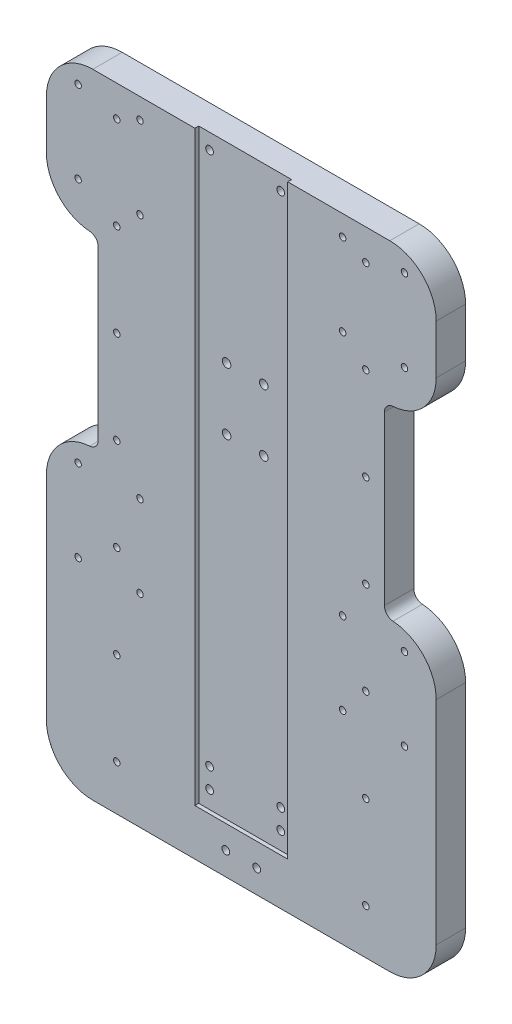
SolidWorks part; units mm, degrees
ref_plane "Piano frontale" through (0, 0, 0) normal (0, 0, 1) x (1, 0, 0)
ref_plane "Piano superiore" through (0, 0, 0) normal (0, 1, 0) x (1, 0, 0)
ref_plane "Piano destro" through (0, 0, 0) normal (1, 0, 0) x (0, 0, -1)
sketch "Schizzo1" plane through (0, 0, 0) normal (0, 0, 1) x (1, 0, 0)
  line L1 (126, -250) -> (-126, -250)
  line L2 (126, -250) -> (126, 250)
  line L3 (126, 250) -> (-126, 250)
  line L4 (-126, -250) -> (-126, 250)
  line L5 (126, -250) -> (-126, 250) construction
  line L6 (126, 250) -> (-126, -250) construction
  point P0 (0, 0)
  dimension "D1" = 252
  dimension "D2" = 500
extrude "Estrusione-Estrusione1" add sketch "Schizzo1" along normal blind 19
sketch "Schizzo2" plane through (0, 0, 19) normal (0, 0, 1) x (1, 0, 0)
  line L0 (1265.2426, 21.4119) -> (-695.7574, 21.4119) construction
  line L1 (1265.2426, 13.5541) -> (-695.7574, 13.5541) construction
  line L2 (1265.2426, 53.5541) -> (-695.7574, 53.5541) construction
  line L3 (1265.2426, 61.4119) -> (-695.7574, 61.4119) construction
  line L4 (-126, 250) -> (-126, -250)
  line L5 (-126, -250) -> (126, -250)
  line L6 (126, -250) -> (126, 250)
  line L7 (126, 250) -> (-126, 250)
  line L8 (-126, 250) -> (-126, -250) construction
  line L9 (-126, -250) -> (126, -250) construction
  line L10 (126, -250) -> (126, 250) construction
  line L11 (126, 250) -> (-126, 250) construction
  line L12 (1265.2426, 21.4119) -> (-695.7574, 21.4119) construction
  line L13 (1265.2426, 13.5541) -> (-695.7574, 13.5541) construction
  line L14 (1265.2426, 53.5541) -> (-695.7574, 53.5541) construction
  line L15 (1265.2426, 61.4119) -> (-695.7574, 61.4119) construction
  line L16 (126, -45.017) -> (-126, -45.017) construction
  line L17 (126, -25.017) -> (-126, -25.017) construction
  line L18 (126, -45.017) -> (-126, -45.017) construction
  line L19 (126, -25.017) -> (-126, -25.017) construction
  line L20 (-126, -45.017) -> (-126, -25.017) construction
  line L21 (126, -35.017) -> (-126, -35.017) construction
  line L22 (-126, -45.017) -> (126, -45.017) construction
  line L23 (-126, -45.017) -> (-126, -25.017) construction
  line L24 (-126, -25.017) -> (126, -25.017) construction
  line L25 (126, -45.017) -> (126, -25.017) construction
  circle A0 centre (110, 17.483) radius 3.9289
  circle A1 centre (110, 57.483) radius 3.9289
  circle A2 centre (-110, 17.483) radius 3.9289
  circle A3 centre (-110, 57.483) radius 3.9289
  circle A4 centre (110, -35.017) radius 3.5
  circle A5 centre (-110, -35.017) radius 3.5
  circle A6 centre (55, -35.017) radius 3.5
  circle A8 centre (-55, -35.017) radius 3.5
  circle A9 centre (20, -35.017) radius 3.5
  circle A10 centre (-20, -35.017) radius 3.5
  circle A11 centre (165, -35.017) radius 3.5 [skipped]
  dimension "D2" = 16
  dimension "D3" = 7.8579
  dimension "D4" = 16
  dimension "D5" = 7.8579
  dimension "D6" = 7
  dimension "D7" = 7
  dimension "D8" = 2
  dimension "D1" = 0
  dimension "D9" = 2
  dimension "D10" = 2
  dimension "D11" = 2
sketch "Schizzo3" plane through (0, 250, 0) normal (0, 1, 0) x (1, 0, 0)
  line L0 (126, -19) -> (-126, -19) construction
  line L1 (30, -16.5) -> (-30, -16.5)
  line L2 (30, -16.5) -> (30, -19)
  line L3 (30, -19) -> (-30, -19)
  line L4 (-30, -16.5) -> (-30, -19)
  line L5 (126, -19) -> (126, 0) construction
  line L6 (-126, -19) -> (-126, 0) construction
  line L7 (126, -19) -> (-126, -19) construction
  dimension "D1" = 2.5
  dimension "D2" = 96
  dimension "D3" = 96
extrude "Taglio-Estrusione1" cut sketch "Schizzo3" against normal through all
sketch "Schizzo4" plane through (0, 0, 16.5) normal (0, 0, 1) x (1, 0, 0)
  line L0 (30, -250) -> (30, 250) construction
  line L2 (30, 250) -> (-30, 250) construction
  line L3 (30, -250) -> (30, 250) construction
  line L6 (-30, 250) -> (-126, 250) construction
  line L7 (-30, -250) -> (-30, 250) construction
  point P11 (23, -118)
  point P14 (-23, -118)
  point P15 (-23, -105)
  point P16 (23, -105)
  point P17 (23, 240)
  point P18 (-23, 240)
  dimension "D1" = 46
  dimension "D2" = 13
  dimension "D3" = 13
  dimension "D4" = 46
  dimension "D5" = 7
  dimension "D6" = 345
  dimension "D7" = 10
  dimension "D8" = 46
  dimension "D9" = 7
  dimension "D10" = 10
  dimension "D11" = 7
  dimension "D12" = 7
sketch "Schizzo5" plane through (0, 0, 19) normal (0, 0, 1) x (1, 0, 0)
  point P4 (80.5006, 170)
  point P7 (80.5006, 110)
  point P16 (80.5006, 50)
  point P17 (80.5006, -10)
  point P18 (80.5006, -70)
  point P19 (80.5006, -130)
  point P20 (80.5006, 230)
hole_wizard "Tap Drill for M5 Tap2" positions "Sketch7" profile "Sketch8" hole size "M5" standard "ISO"
sketch "Sketch7" plane through (0, 0, 19) normal (0, 0, 1) x (1, 0, 0)
  point P0 (80.5006, -130)
  point P3 (80.5006, -70)
  point P7 (80.5006, -10)
  point P10 (80.5006, 50)
  point P13 (80.5006, 110)
  point P16 (80.5006, 170)
  point P19 (80.5006, 230)
sketch "Sketch8" plane through (80.5006, -130, 19) normal (1, 0, 0) x (0, -1, 0)
  line L0 (0, 0) -> (0, 37.8618)
  line L1 (0, 37.8618) -> (2.1, 36.6)
  line L2 (2.1, 36.6) -> (2.1, 0)
  line L5 (2.1, 0) -> (0, 0)
  line L10 (0, 37.8618) -> (-2.1, 36.6) construction
  line L11 (0, -6.35) -> (0, 107.95) construction
  dimension "Hole Dia." = 4.2
  dimension "Hole Depth" = 36.6
  dimension "Drill Angle" = 118
sketch "Schizzo6" plane through (0, 0, 19) normal (0, 0, 1) x (1, 0, 0)
  line L0 (126, -250) -> (126, 250) construction
  line L2 (126, 250) -> (30, 250) construction
  point P23 (108, 172.8083)
  point P26 (63, 172.8083)
  point P27 (63, 229.8083)
  point P28 (108, 229.8083)
  dimension "D1" = 45
  dimension "D2" = 45
  dimension "D3" = 57
  dimension "D4" = 57
  dimension "D5" = 18
  dimension "D6" = 20.1917
  dimension "D7" = 20.1917
  dimension "D8" = 18
hole_wizard "Tap Drill for M5 Tap1" positions "Sketch14" profile "Sketch15" hole size "M5" standard "ISO"
sketch "Sketch14" plane through (0, 0, 19) normal (0, 0, 1) x (1, 0, 0)
  line L1 (105.5, 183.8083) -> (65.5, 183.8083)
  line L2 (105.5, 183.8083) -> (105.5, 236.8083)
  line L3 (105.5, 236.8083) -> (65.5, 236.8083)
  line L4 (65.5, 183.8083) -> (65.5, 236.8083)
  line L6 (105.5, -28.1917) -> (65.5, -28.1917)
  line L7 (105.5, -28.1917) -> (105.5, 24.8083)
  line L8 (105.5, 24.8083) -> (65.5, 24.8083)
  line L9 (65.5, -28.1917) -> (65.5, 24.8083)
  line L10 (85.5, -28.1917) -> (85.5, 236.8083) construction
  line L12 (105.5, 210.3083) -> (65.5, 210.3083) construction
  line L14 (105.5, -1.6917) -> (65.5, -1.6917) construction
  line L16 (108, 172.8083) -> (63, 172.8083) construction
  line L18 (85.5, 256.2745) -> (85.5, -301.4126) construction
  point P19 (105.5, 236.8083)
  point P21 (65.5, 236.8083)
  point P23 (105.5, 183.8083)
  point P25 (65.5, 183.8083)
  point P99 (105.5, -28.1917)
  point P102 (65.5, -28.1917)
  point P105 (65.5, 24.8083)
  point P108 (105.5, 24.8083)
  dimension "D1" = 40
  dimension "D2" = 53
  dimension "D3" = 40
  dimension "D4" = 53
sketch "Sketch15" plane through (105.5, 236.8083, 19) normal (1, 0, 0) x (0, -1, 0)
  line L0 (0, 0) -> (0, 37.8618)
  line L1 (0, 37.8618) -> (2.1, 36.6)
  line L2 (2.1, 36.6) -> (2.1, 0)
  line L5 (2.1, 0) -> (0, 0)
  line L10 (0, 37.8618) -> (-2.1, 36.6) construction
  line L11 (0, -6.35) -> (0, 107.95) construction
  dimension "Hole Dia." = 4.2
  dimension "Hole Depth" = 36.6
  dimension "Drill Angle" = 118
hole_wizard "Tap Drill for M6 Tap4" positions "Sketch9" profile "Sketch10" hole size "M6" standard "ISO"
sketch "Sketch9" plane through (0, 0, 16.5) normal (0, 0, 1) x (1, 0, 0)
  point P0 (23, -118)
  point P3 (23, -105)
  point P6 (-23, -118)
  point P9 (-23, -105)
  point P12 (23, 240)
  point P15 (-23, 240)
sketch "Sketch10" plane through (23, -118, 16.5) normal (1, 0, 0) x (0, -1, 0)
  line L0 (0, 0) -> (0, 38.1022)
  line L1 (0, 38.1022) -> (2.5, 36.6)
  line L2 (2.5, 36.6) -> (2.5, 0)
  line L5 (2.5, 0) -> (0, 0)
  line L10 (0, 38.1022) -> (-2.5, 36.6) construction
  line L11 (0, -6.35) -> (0, 107.95) construction
  dimension "Hole Dia." = 5
  dimension "Hole Depth" = 36.6
  dimension "Drill Angle" = 118
sketch "Sketch11" plane through (0, 0, 16.5) normal (0, 0, 1) x (1, 0, 0)
  line L0 (0, -250) -> (0, 250) construction
  line L1 (30, -250) -> (-30, -250) construction
  line L2 (30, 250) -> (-30, 250) construction
ref_plane "Plane1" through (0, 0, 0) normal (-1, 0, 0) x (0, 0, 1)
mirror "Mirror1" about plane through (0, 0, 0) normal (-1, 0, 0) of "Tap Drill for M5 Tap2"
mirror "Mirror2" about plane through (0, 0, 0) normal (-1, 0, 0) of "Tap Drill for M5 Tap1"
sketch "Sketch16" plane through (0, 0, 0) normal (0, 0, -1) x (-1, 0, 0)
  line L0 (126, 250) -> (126, -250) construction
  line L1 (126, -317.9299) -> (-126, -317.9299)
  line L2 (126, -317.9299) -> (126, -159.25)
  line L3 (126, -159.25) -> (-126, -159.25)
  line L4 (-126, -317.9299) -> (-126, -159.25)
  line L5 (-126, -250) -> (-126, 250) construction
  line L9 (-12.9, -159.25) -> (25.2, -159.25) construction
extrude "Cut-Extrude1" cut sketch "Sketch16" against normal blind 28
sketch "Sketch26" plane through (0, 0, 16.5) normal (0, 0, 1) x (1, 0, 0)
  line L0 (30, -159.25) -> (30, 250) construction
  line L1 (-30, -159.25) -> (30, -159.25)
  line L2 (-30, -159.25) -> (-30, -129.25)
  line L3 (-30, -129.25) -> (30, -129.25)
  line L4 (30, -159.25) -> (30, -129.25)
  dimension "D1" = 30
extrude "Boss-Extrude1" add sketch "Sketch26" along normal up to surface (2.5 mm away) up to face at (-78, 45.375, 19)
hole_wizard "M5 Clearance Hole1" positions "Sketch17" profile "Sketch18" hole size "M5" standard "ISO" end condition through all
sketch "Sketch17" plane through (0, 0, 16.5) normal (0, 0, 1) x (1, 0, 0)
  line L0 (12, 86.3083) -> (-12, 126.3083) construction
  line L1 (-12, 126.3083) -> (-12, 86.3083) construction
  line L2 (-12, 86.3083) -> (12, 126.3083) construction
  line L3 (12, 126.3083) -> (12, 86.3083) construction
  line L4 (12, 86.3083) -> (-12, 86.3083) construction
  line L7 (-12, 126.3083) -> (12, 126.3083) construction
  point P0 (-12, 86.3083)
  point P2 (12, 86.3083)
  point P4 (12, 126.3083)
  point P6 (-12, 126.3083)
  dimension "D1" = 40
  dimension "D2" = 24
sketch "Sketch18" plane through (-12, 86.3083, 16.5) normal (1, 0, 0) x (0, -1, 0)
  line L0 (0, 0) -> (0, 16.5)
  line L1 (0, 16.5) -> (2.75, 16.5)
  line L2 (2.75, 16.5) -> (2.75, 0)
  line L5 (2.75, 0) -> (0, 0)
  line L11 (0, -6.35) -> (0, 107.95) construction
  dimension "Thru Hole Dia." = 5.5
  dimension "Thru Hole Depth" = 16.5
sketch "Sketch19" plane through (0, -195.45, 0) normal (0, -1, 0) x (-1, 0, 0)
  line L0 (0, -70.7) -> (0, 68.239) construction
  line L1 (126, -9.5) -> (-126, -9.5) construction
  line L2 (126, -19) -> (126, 0) construction
  line L3 (-126, -19) -> (-126, 0) construction
  line L5 (28.2, 0) -> (-28.2, 0) construction
  point P8 (20, -9.5)
  point P9 (-20, -9.5)
  point P12 (-20, 9.5)
  point P13 (20, 9.5)
  dimension "D1" = 20
hole_wizard "Tap Drill for M6 Tap2" positions "Sketch22" profile "Sketch23" hole size "M6" standard "ISO"
sketch "Sketch22" plane through (0, -159.25, 0) normal (0, -1, 0) x (-1, 0, 0)
  point P0 (20, -7.125)
  point P2 (-20, -7.125)
sketch "Sketch23" plane through (-20, -159.25, 7.125) normal (1, 0, 0) x (0, 0, -1)
  line L0 (0, 0) -> (0, 31.5022)
  line L1 (0, 31.5022) -> (2.5, 30)
  line L2 (2.5, 30) -> (2.5, 0)
  line L5 (2.5, 0) -> (0, 0)
  line L10 (0, 31.5022) -> (-2.5, 30) construction
  line L11 (0, -6.35) -> (0, 107.95) construction
  dimension "Hole Dia." = 5
  dimension "Hole Depth" = 30
  dimension "Drill Angle" = 118
hole_wizard "Tap Drill for M6 Tap3" positions "Sketch24" profile "Sketch25" hole size "M6" standard "ISO" end condition through all
sketch "Sketch24" plane through (0, 0, 0) normal (0, 0, -1) x (-1, 0, 0)
  point P0 (-10, -144.25)
  point P6 (10, -144.25)
sketch "Sketch25" plane through (10, -144.25, 0) normal (1, 0, 0) x (0, 1, 0)
  line L0 (0, 0) -> (0, 19)
  line L1 (0, 19) -> (2.5, 19)
  line L2 (2.5, 19) -> (2.5, 0)
  line L5 (2.5, 0) -> (0, 0)
  line L11 (0, -6.35) -> (0, 107.95) construction
  dimension "Thru Hole Dia." = 5
  dimension "Thru Hole Depth" = 19
sketch "Sketch27" plane through (0, 0, 19) normal (0, 0, 1) x (1, 0, 0)
  line L2 (-126, 38.082) -> (-126, 158.222)
  line L4 (-92.5, 38.082) -> (-92.5, 158.222)
  line L5 (-126, 38.082) -> (-92.5, 38.082)
  line L7 (-126, 158.222) -> (-92.5, 158.222)
  line L9 (-92.5, 40.082) -> (-92.5, 156.222) construction
  line L10 (-126, 40.082) -> (-126, 156.222) construction
  line L11 (-128, 158.222) -> (-90.5, 158.222) construction
  line L12 (-128, 38.082) -> (-128, 158.222) construction
  line L13 (-128, 38.082) -> (-90.5, 38.082) construction
  line L14 (-126, 40.082) -> (-92.5, 40.082) construction
  line L15 (-90.5, 38.082) -> (-90.5, 158.222) construction
  line L16 (-126, 156.222) -> (-92.5, 156.222) construction
  line L17 (-126, 98.152) -> (126, 98.152) construction
  line L18 (126, -159.25) -> (126, 250) construction
  line L19 (126, 98.152) -> (0, 98.152) construction
  line L20 (0, 98.152) -> (0, 87.9155) construction
  line L21 (-126, 38.082) -> (-92.5, 38.082)
  line L22 (-126, 158.222) -> (-92.5, 158.222)
  line L23 (126, 158.222) -> (92.5, 158.222)
  line L24 (126, 38.082) -> (92.5, 38.082)
  line L25 (126, 158.222) -> (92.5, 158.222)
  line L26 (126, 38.082) -> (92.5, 38.082)
  line L27 (92.5, 38.082) -> (92.5, 158.222)
  line L28 (126, 38.082) -> (126, 158.222)
  line M11 (-126, 250) -> (-126, -159.25)
  line M13 (126, -159.25) -> (126, 250)
  dimension "D1" = 2
extrude "Cut-Extrude2" cut sketch "Sketch27" against normal blind 76.9911 contours L27 L24 L23 M13 | L7 L5 L4 M11
fillet "Fillet1" radius 30 4 edges at (126, 158.222, 9.5) (126, 38.082, 9.5) (-126, 158.222, 9.5) (-126, 38.082, 9.5)
fillet "Fillet2" radius 30 4 edges at (126, 250, 9.5) (-126, 250, 9.5) (-126, -159.25, 9.5) (126, -159.25, 9.5)
fillet "Fillet3" radius 6 4 edges at (92.5, 158.222, 9.5) (92.5, 38.082, 9.5) (-92.5, 38.082, 9.5) (-92.5, 158.222, 9.5)
sketch "Sketch28" plane through (0, 0, 0) normal (0, 0, -1) x (-1, 0, 0)
  line L0 (-32, 106.3083) -> (32, 106.3083) construction
  line L4 (32, 78.3083) -> (-32, 78.3083)
  line L5 (32, 78.3083) -> (32, 134.3083)
  line L6 (32, 134.3083) -> (-32, 134.3083)
  line L7 (-32, 78.3083) -> (-32, 134.3083)
  line L8 (0, -10.45) -> (0, 10.45) construction
  circle A0 centre (-12, 86.3083) radius 2.75 construction
  circle A1 centre (-12, 86.3083) radius 2.75 construction
  dimension "D4" = 32
  dimension "D1" = 32
  dimension "D2" = 28
extrude "Cut-Extrude3" cut sketch "Sketch28" against normal blind 2
sketch "Sketch29" plane through (0, 0, 2) normal (0, 0, -1) x (-1, 0, 0)
  line L0 (12, 86.3083) -> (12, 79.3083) construction
  line L1 (-17.5, 82.3083) -> (17.5, 82.3083)
  line L2 (-17.5, 82.3083) -> (-17.5, 130.3083)
  line L3 (-17.5, 130.3083) -> (17.5, 130.3083)
  line L4 (17.5, 82.3083) -> (17.5, 130.3083)
  circle A0 centre (12, 86.3083) radius 2.6
  circle A1 centre (-12, 86.3083) radius 2.6
  circle A2 centre (12, 126.3083) radius 2.6
  circle A3 centre (-12, 126.3083) radius 2.6
  circle A4 centre (12, 79.3083) radius 0.5
  circle A5 centre (-12, 79.3083) radius 0.5
  circle A6 centre (12, 119.3083) radius 0.5
  circle A7 centre (-12, 119.3083) radius 0.5
  dimension "D1" = 5.2
  dimension "D2" = 5.2
  dimension "D3" = 5.2
  dimension "D4" = 5.2
  dimension "D5" = 1
  dimension "D6" = 1
  dimension "D7" = 1
  dimension "D8" = 1
  dimension "D9" = 7
equation "\"D3@Schizzo3\"=\"D2@Schizzo3\""
equation "\"D11@Schizzo4\"=\"D5@Schizzo4\""
